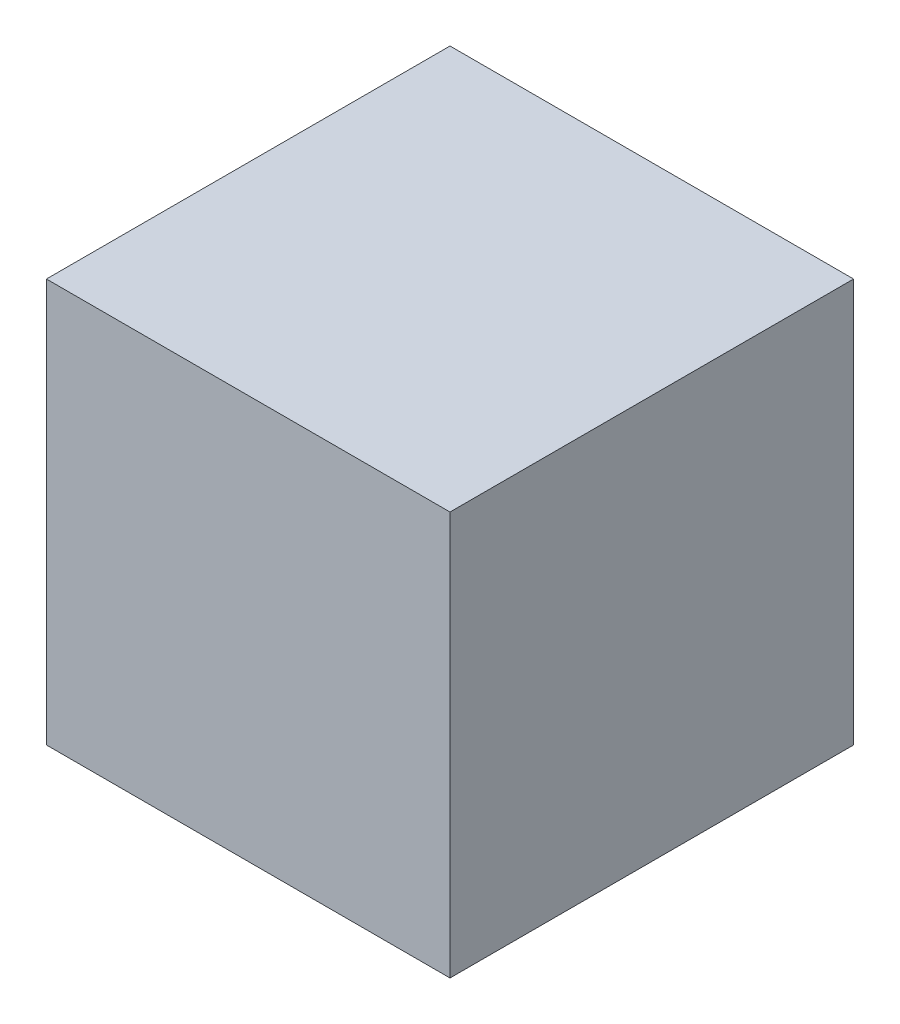
SolidWorks part; units mm, degrees
ref_plane "Front Plane" through (0, 0, 0) normal (0, 0, 1) x (1, 0, 0)
ref_plane "Top Plane" through (0, 0, 0) normal (0, 1, 0) x (1, 0, 0)
ref_plane "Right Plane" through (0, 0, 0) normal (1, 0, 0) x (0, 0, -1)
sketch "Sketch1" plane through (0, 0, 0) normal (0, 1, 0) x (1, 0, 0)
  line L1 (-75, 75) -> (75, 75)
  line L2 (-75, 75) -> (-75, -75)
  line L3 (-75, -75) -> (75, -75)
  line L4 (75, 75) -> (75, -75)
  line L5 (-75, 75) -> (75, -75) construction
  line L6 (-75, -75) -> (75, 75) construction
  point P0 (0, 0)
  dimension "D1" = 150
  dimension "D2" = 150
extrude "Boss-Extrude1" add sketch "Sketch1" along normal blind 150
